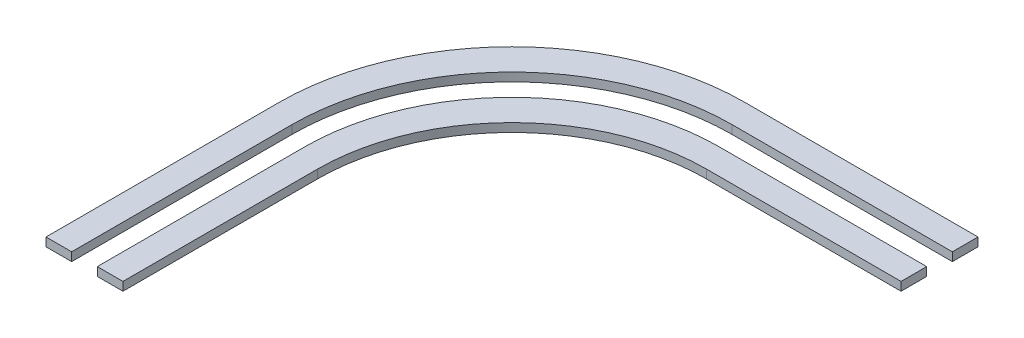
SolidWorks part; units mm, degrees
ref_plane "Front Plane" through (0, 0, 0) normal (0, 0, 1) x (1, 0, 0)
ref_plane "Top Plane" through (0, 0, 0) normal (0, 1, 0) x (1, 0, 0)
ref_plane "Right Plane" through (0, 0, 0) normal (1, 0, 0) x (0, 0, -1)
sketch "Sketch2" plane through (0, 0, 0) normal (0, 1, 0) x (1, 0, 0)
  line L0 (125, 0) -> (125, 437.5)
  line L1 (0, 0) -> (1000, 0)
  line L2 (0, 0) -> (0, 1000)
  line L3 (0, 1000) -> (1000, 1000)
  line L4 (1000, 0) -> (1000, 1000)
  line L5 (562.5, 875) -> (1000, 875)
  line L8 (875, 0) -> (875, 62.5)
  line L9 (937.5, 125) -> (1000, 125)
  line L10 (500, 0) -> (500, 250)
  line L11 (750, 500) -> (1000, 500)
  line L12 (485, 0) -> (485, 257.5)
  line L13 (742.5, 515) -> (1000, 515)
  line L14 (515, 0) -> (515, 242.5)
  line L15 (757.5, 485) -> (1000, 485)
  line L17 (1000, 0) -> (455, 0)
  line L18 (1000, 0) -> (1000, 545)
  line L19 (1000, 545) -> (727.5, 545)
  line L20 (455, 0) -> (455, 272.5)
  line L21 (1000, 0) -> (545, 0)
  line L22 (1000, 0) -> (1000, 455)
  line L23 (1000, 455) -> (772.5, 455)
  line L24 (545, 0) -> (545, 227.5)
  arc A5 (937.5, 125) -> (875, 62.5) centre (937.5, 62.5) ccw
  arc A9 (750, 500) -> (500, 250) centre (750, 250) ccw
  arc A10 (562.5, 875) -> (125, 437.5) centre (562.5, 437.5) ccw
  arc A13 (742.5, 515) -> (485, 257.5) centre (742.5, 257.5) ccw
  arc A14 (757.5, 485) -> (515, 242.5) centre (757.5, 242.5) ccw
  arc A15 (727.5, 545) -> (455, 272.5) centre (727.5, 272.5) ccw
  arc A18 (772.5, 455) -> (545, 227.5) centre (772.5, 227.5) ccw
  dimension "D1" = 485
  dimension "D2" = 125
  dimension "D3" = 375
  dimension "D4" = 375
  dimension "D5" = 375
  dimension "D6" = 375
  dimension "D7" = 515
  dimension "D8" = 30
  dimension "D9" = 30
  dimension "D10" = 30
  dimension "D11" = 30
extrude "Boss-Extrude1" add sketch "Sketch2" along normal blind 10 contours L19 A15 L20 L1 L12 A13 L13 L4 | A18 L23 L18 L15 A14 L14 L1 L24
equation "\"Scale\"= 8"
equation "\"Tile Size\"= \"Road Size\" * 2"
equation "\"Road Size\"= \"Real Lane Size\" * 2 / \"Scale\""
equation "\"Real Lane Size\"= 3m"
